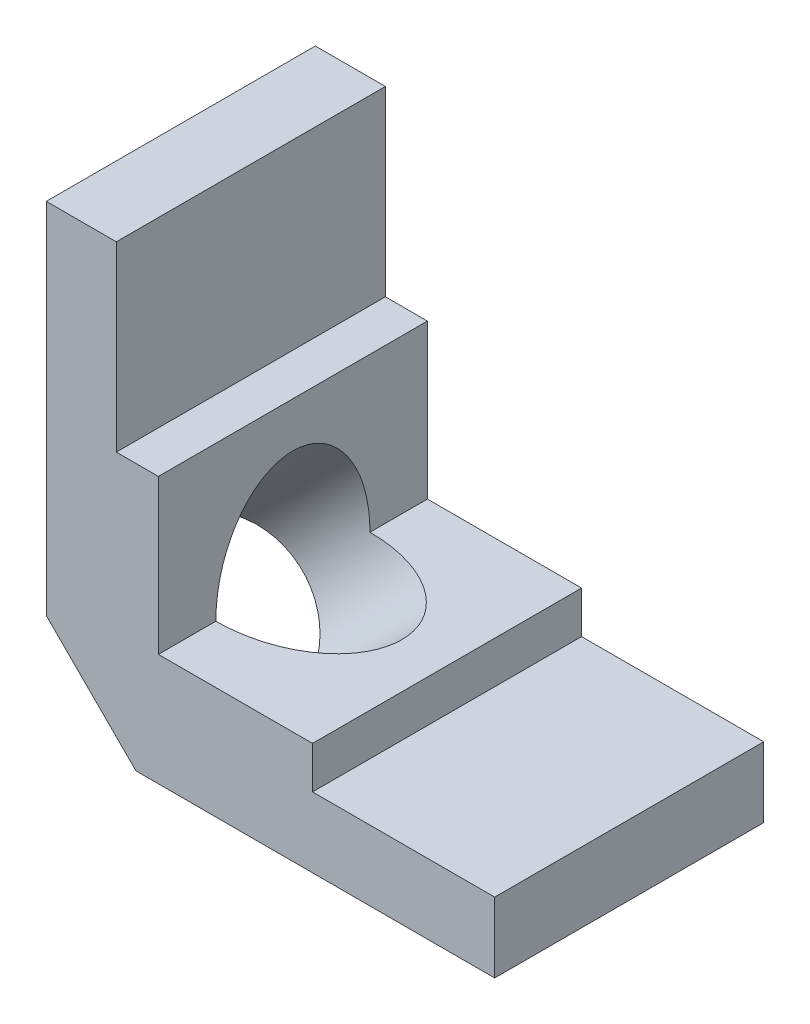
SolidWorks part; units mm, degrees
ref_plane "Front Plane" through (0, 0, 0) normal (0, 0, 1) x (1, 0, 0)
ref_plane "Top Plane" through (0, 0, 0) normal (0, 1, 0) x (1, 0, 0)
ref_plane "Right Plane" through (0, 0, 0) normal (1, 0, 0) x (0, 0, -1)
sketch "Sketch1" plane through (0, 0, 0) normal (0, 0, 1) x (1, 0, 0)
  line L0 (0, 0) -> (0, 25.4)
  line L1 (0, 25.4) -> (6.35, 25.4)
  line L2 (6.35, 25.4) -> (6.35, 6.35)
  line L3 (6.35, 6.35) -> (25.4, 6.35)
  line L4 (25.4, 6.35) -> (25.4, 0)
  line L5 (25.4, 0) -> (0, 0)
  dimension "D1" = 6.35
  dimension "D2" = 25.4
extrude "Boss-Extrude1" add sketch "Sketch1" along normal mid plane 15.24
sketch "Sketch2" plane through (6.35, 0, 0) normal (1, 0, 0) x (0, 0, -1)
  line L0 (-7.62, 6.35) -> (-7.62, 25.4) construction
  line L1 (-7.62, 25.4) -> (7.62, 25.4)
  line L2 (-7.62, 25.4) -> (-7.62, 15.0812)
  line L3 (-7.62, 15.0812) -> (7.62, 15.0812)
  line L4 (7.62, 25.4) -> (7.62, 15.0812)
  line L5 (-7.62, 6.35) -> (7.62, 6.35) construction
  dimension "edge" = 8.7312
extrude "Cut-Extrude1" cut sketch "Sketch2" against normal blind 2.3813
sketch "Sketch4" plane through (0, 6.35, 0) normal (0, 1, 0) x (1, 0, 0)
  line L0 (25.4, -7.62) -> (6.35, -7.62) construction
  line L1 (15.0813, -7.62) -> (25.4, -7.62)
  line L2 (15.0813, -7.62) -> (15.0813, 7.62)
  line L3 (15.0813, 7.62) -> (25.4, 7.62)
  line L4 (25.4, -7.62) -> (25.4, 7.62)
  line L5 (25.4, 7.62) -> (6.35, 7.62) construction
  line L7 (6.35, -7.62) -> (6.35, 7.62) construction
extrude "Cut-Extrude2" cut sketch "Sketch4" against normal blind 2.3813
chamfer "Chamfer1" distance 5.08 angle 45 1 edges at (0, 0, 0)
hole_wizard "11/32 (0.34375) Diameter Hole1" positions "Sketch9" profile "Sketch10" hole size "11/32" standard "Ansi Inch" end condition through all
sketch "Sketch9" plane through (2.54, 2.54, 0) normal (-0.7071, -0.7071, 0) x (0, 0, 1)
  line L1 (-7.62, 3.5921) -> (7.62, -3.5921)
  line L3 (7.62, 3.5921) -> (-7.62, -3.5921)
  point P0 (0, 0)
sketch "Sketch10" plane through (2.54, 2.54, 0) normal (0, 0, 1) x (0.7071, -0.7071, 0)
  line L0 (0, 0) -> (0, 32.3289)
  line L1 (0, 32.3289) -> (4.3656, 32.3289)
  line L2 (4.3656, 32.3289) -> (4.3656, 0)
  line L5 (4.3656, 0) -> (0, 0)
  line L11 (0, -6.35) -> (0, 107.95) construction
  dimension "Thru Hole Dia." = 8.7312
  dimension "Thru Hole Depth" = 32.3289
